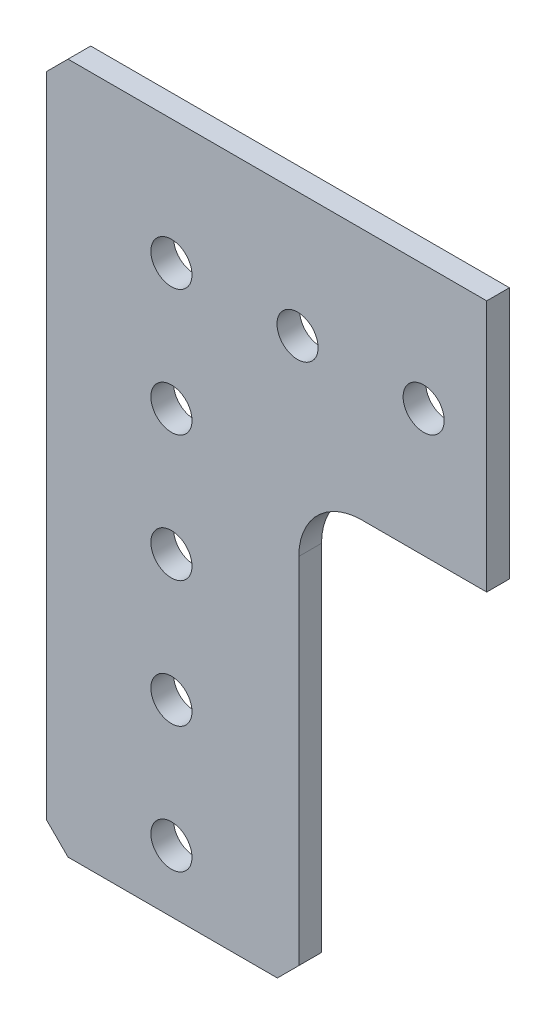
SolidWorks part; units mm, degrees
ref_plane "Front Plane" through (0, 0, 0) normal (0, 0, 1) x (1, 0, 0)
ref_plane "Top Plane" through (0, 0, 0) normal (0, 1, 0) x (1, 0, 0)
ref_plane "Right Plane" through (0, 0, 0) normal (1, 0, 0) x (0, 0, -1)
ref_plane "Plane1" through (0, 0, 0) normal (0, 0, -1) x (-1, 0, 0)
sketch "Sketch1" plane through (0, 0, 0) normal (0, 0, -1) x (-1, 0, 0)
  line L0 (10.414, 12.573) -> (-54.864, 12.573)
  line L1 (-54.864, 12.573) -> (-57.023, 10.414)
  line L2 (-57.023, 10.414) -> (-57.023, -10.668)
  line L3 (-57.023, -10.668) -> (-54.864, -12.827)
  line L4 (-54.864, -12.827) -> (-19.177, -12.827)
  line L5 (-12.827, -19.177) -> (-12.827, -54.864)
  line L6 (-12.827, -54.864) -> (-10.668, -57.023)
  line L7 (-10.668, -57.023) -> (10.414, -57.023)
  line L8 (10.414, -57.023) -> (12.573, -54.864)
  line L9 (12.573, -54.864) -> (12.573, 10.414)
  line L10 (12.573, 10.414) -> (10.414, 12.573)
  arc A0 (-19.177, -12.827) -> (-12.827, -19.177) centre (-19.177, -19.177) cw
  circle A1 centre (0, -50.8) radius 2.0701
  circle A2 centre (0, -25.4) radius 2.0701
  circle A3 centre (-38.1, 0) radius 2.0701
  circle A4 centre (-12.7, 0) radius 2.0701
  circle A5 centre (0, 0) radius 2.0701
  circle A6 centre (-25.4, 0) radius 2.0701
  circle A7 centre (0, -12.7) radius 2.0701
  circle A8 centre (0, -38.1) radius 2.0701
  circle A9 centre (-50.8, 0) radius 2.0701
extrude "Boss-Extrude1" add sketch "Sketch1" against normal blind 2.286
sketch "Sketch2" plane through (0, 0, 2.286) normal (0, 0, 1) x (1, 0, 0)
  line L0 (-10.414, 12.573) -> (54.864, 12.573) construction
  line L1 (57.023, -12.827) -> (31.75, -12.827)
  line L2 (57.023, -12.827) -> (57.023, 12.573)
  line L3 (57.023, 12.573) -> (31.75, 12.573)
  line L4 (31.75, -12.827) -> (31.75, 12.573)
  line L5 (57.023, 10.414) -> (57.023, -10.668) construction
  circle A0 centre (25.4, 0) radius 2.0701 construction
  dimension "D1" = 6.35
extrude "Cut-Extrude1" cut sketch "Sketch2" against normal through all both and the other way through all
